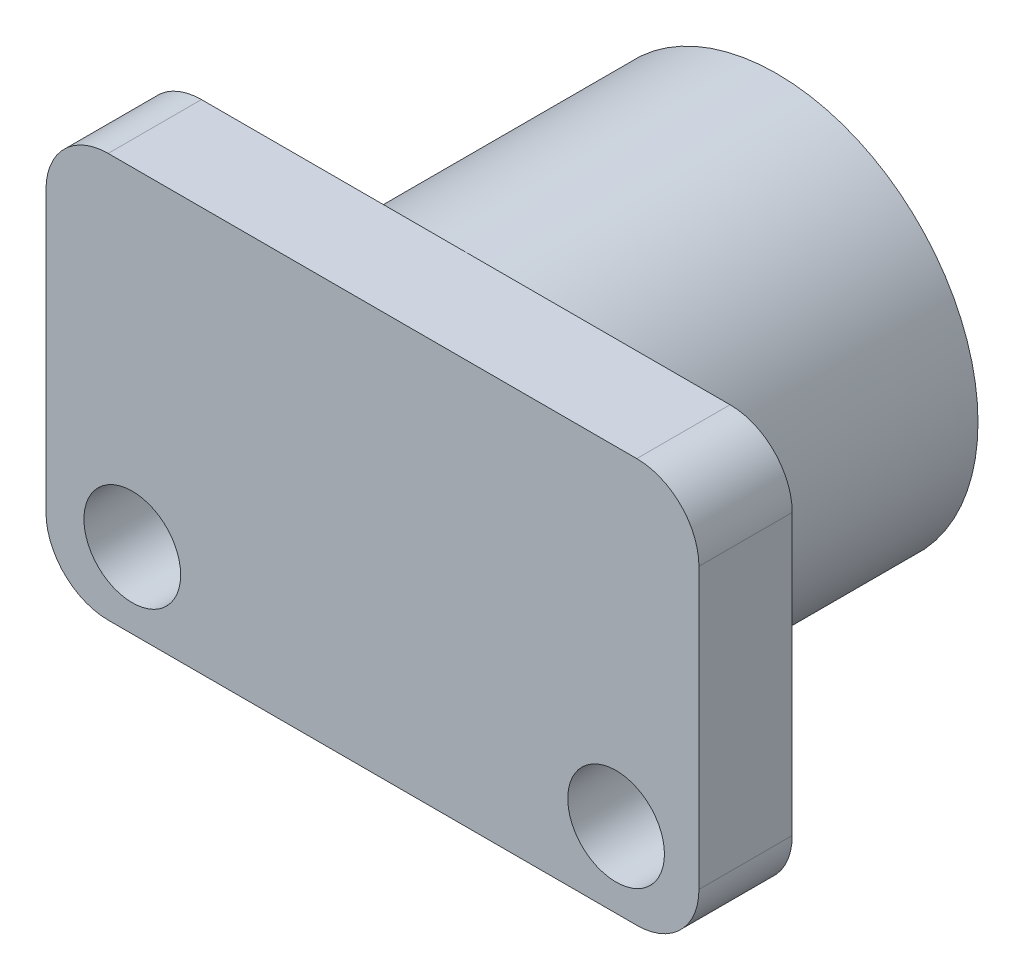
SolidWorks part; units mm, degrees
material "ABS"
ref_plane "Plan de face" through (0, 0, 0) normal (0, 0, 1) x (1, 0, 0)
ref_plane "Plan de dessus" through (0, 0, 0) normal (0, 1, 0) x (1, 0, 0)
ref_plane "Plan de droite" through (0, 0, 0) normal (1, 0, 0) x (0, 0, -1)
sketch "Esquisse1" plane through (0, 0, 0) normal (0, 0, 1) x (1, 0, 0)
  line L1 (10.5, -6.5) -> (-10.5, -6.5)
  line L2 (10.5, -6.5) -> (10.5, 6.5)
  line L3 (10.5, 6.5) -> (-10.5, 6.5)
  line L4 (-10.5, -6.5) -> (-10.5, 6.5)
  line L5 (10.5, -6.5) -> (-10.5, 6.5) construction
  line L6 (10.5, 6.5) -> (-10.5, -6.5) construction
  point P0 (0, 0)
  dimension "D1" = 21
  dimension "D2" = 13
extrude "Boss.-Extru.1" add sketch "Esquisse1" along normal blind 3
fillet "Congé1" radius 2 4 edges at (-10.5, -6.5, 1.5) (10.5, -6.5, 1.5) (10.5, 6.5, 1.5) (-10.5, 6.5, 1.5)
sketch "Esquisse2" plane through (0, 0, 3) normal (0, 0, 1) x (1, 0, 0)
  line L0 (-10.5, 4.5) -> (-10.5, -4.5) construction
  circle A0 centre (-7.725, -4.0741) radius 1.555
  circle A1 centre (7.835, -4.0741) radius 1.555
  dimension "D1" = 3.11
  dimension "D2" = 3.11
  dimension "D3" = 15.56
  dimension "D4" = 2.775
extrude "Enlèv. mat.-Extru.1" cut sketch "Esquisse2" against normal through all
sketch "Esquisse3" plane through (0, 0, 0) normal (0, 0, -1) x (-1, 0, 0)
  circle A0 centre (0, 0) radius 6.475
  dimension "D1" = 12.95
extrude "Boss.-Extru.2" add sketch "Esquisse3" along normal blind 10
sketch "Esquisse4" plane through (0, 0, -10) normal (0, 0, -1) x (-1, 0, 0)
  circle A0 centre (0, 0) radius 5.065
  dimension "D1" = 10.13
extrude "Enlèv. mat.-Extru.2" cut sketch "Esquisse4" against normal blind 10
